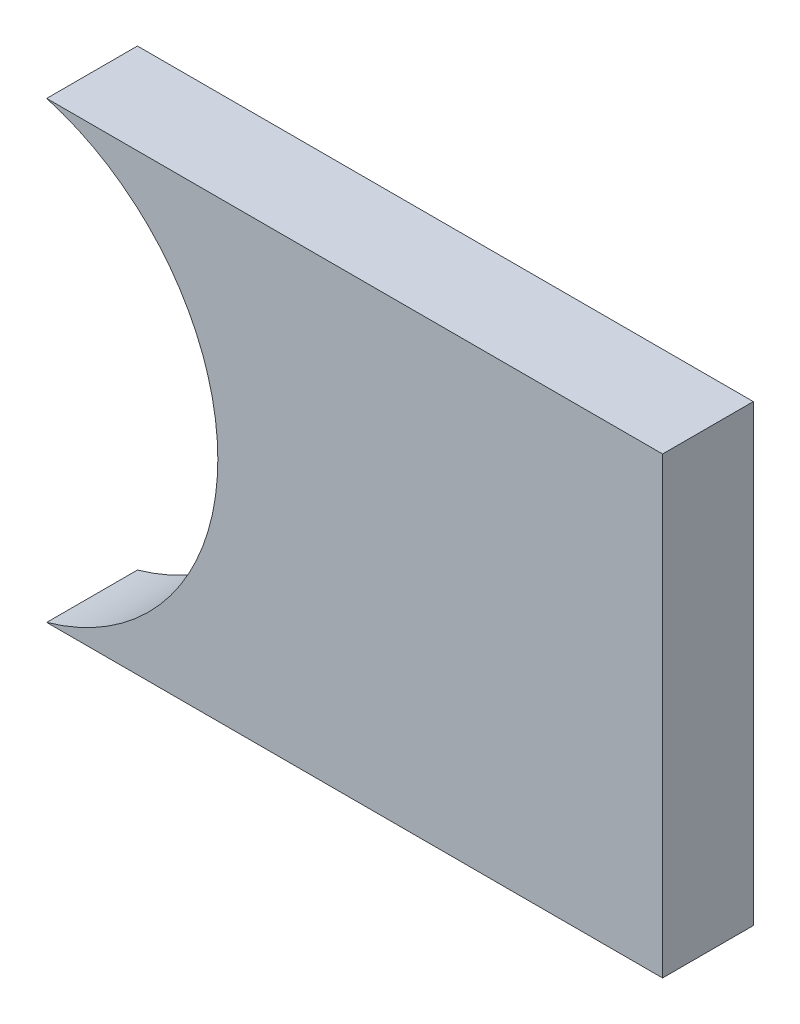
SolidWorks part; units mm, degrees
ref_plane "Front Plane" through (0, 0, 0) normal (0, 0, 1) x (1, 0, 0)
ref_plane "Top Plane" through (0, 0, 0) normal (0, 1, 0) x (1, 0, 0)
ref_plane "Right Plane" through (0, 0, 0) normal (1, 0, 0) x (0, 0, -1)
sketch "Sketch1" plane through (0, 0, 0) normal (0, 0, 1) x (1, 0, 0)
  line L1 (-25.396, -5.4888) -> (-10.396, -5.4888)
  line L2 (-25.396, -5.4888) -> (-25.396, -15.4888)
  line L3 (-25.396, -15.4888) -> (-10.396, -15.4888)
  line L4 (-10.396, -5.4888) -> (-10.396, -15.4888)
  line L5 (-25.396, -5.4888) -> (-25.396, -10.4888)
  circle A0 centre (-25.396, -10.4888) radius 5.2
extrude "Boss-Extrude1" add sketch "Sketch1" along normal blind 2 contours A0 L3 L4 L1
